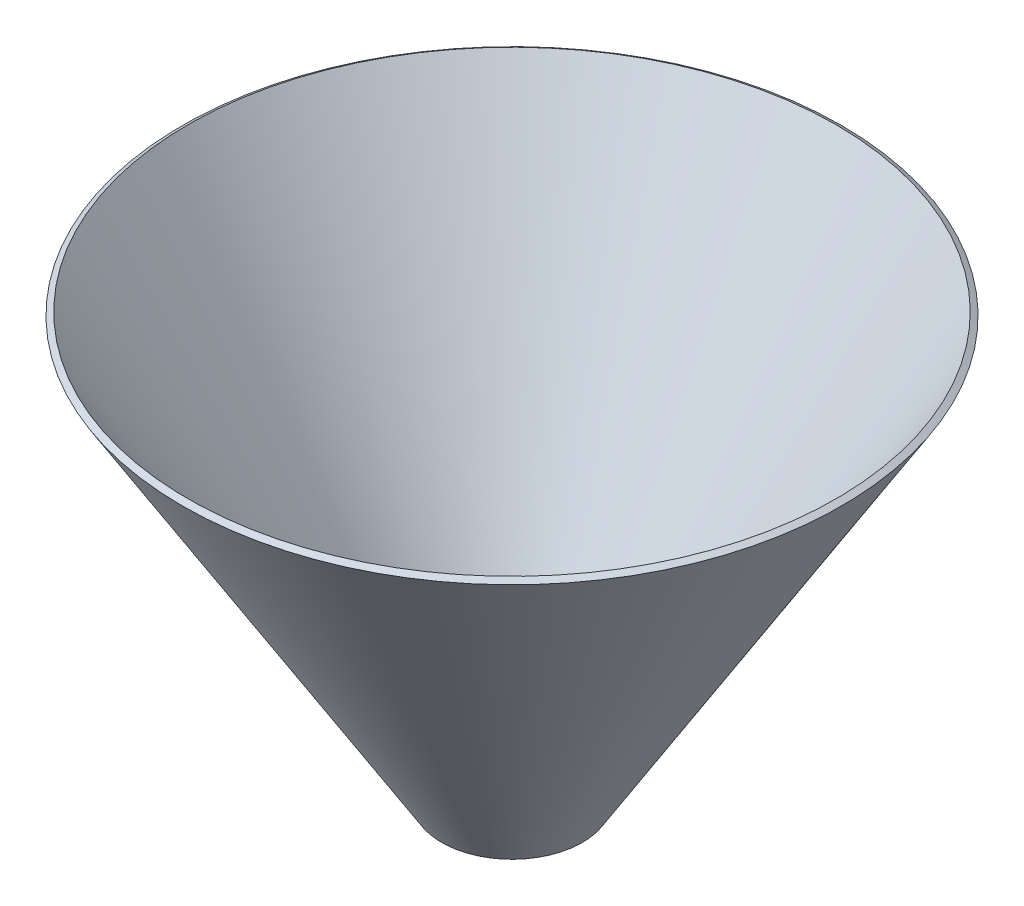
SolidWorks part; units mm, degrees
ref_plane "Front Plane" through (0, 0, 0) normal (0, 0, 1) x (1, 0, 0)
ref_plane "Top Plane" through (0, 0, 0) normal (0, 1, 0) x (1, 0, 0)
ref_plane "Right Plane" through (0, 0, 0) normal (1, 0, 0) x (0, 0, -1)
sketch "Sketch1" plane through (0, 0, 0) normal (0, 0, 1) x (1, 0, 0)
  line L0 (0, 0) -> (0, 64.975) construction
  line L1 (10, 0) -> (50, 64.975)
  line L2 (0, 20) -> (22.3124, 20) construction
  dimension "D1" = 50
  dimension "D2" = 10
  dimension "D3" = 20
  dimension "D4" = 22.3124
revolve "Revolve-Thin1" add sketch "Sketch1" angle 360 about L0
